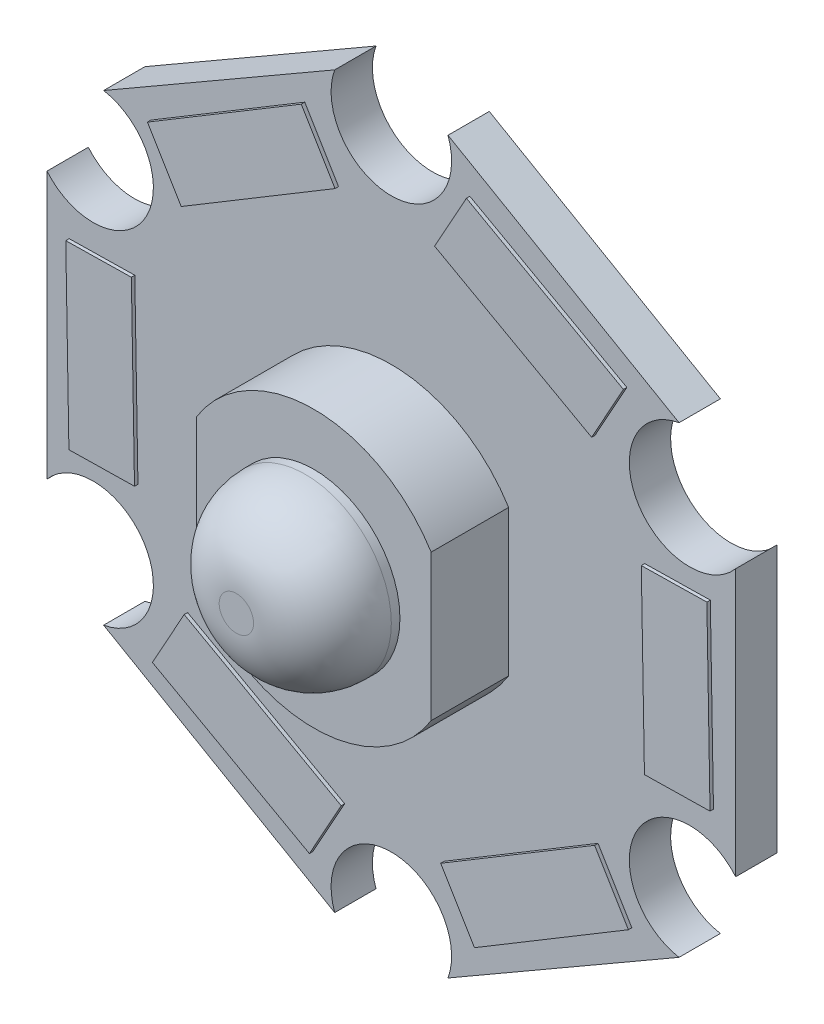
SolidWorks part; units mm, degrees
material "Aleación 1060"
ref_plane "Alzado" through (0, 0, 0) normal (0, 0, 1) x (1, 0, 0)
ref_plane "Planta" through (0, 0, 0) normal (0, 1, 0) x (1, 0, 0)
ref_plane "Vista lateral" through (0, 0, 0) normal (1, 0, 0) x (0, 0, -1)
sketch "Croquis1" plane through (0, 0, 0) normal (0, 0, 1) x (1, 0, 0)
  line L0 (8.6603, 5) -> (-8.6603, -5) construction
  line L1 (-10, 3.8741) -> (-10, -3.8741)
  line L2 (-8.3551, -6.7232) -> (-1.6449, -10.5973)
  line L3 (1.6449, -10.5973) -> (8.3551, -6.7232)
  line L4 (10, -3.8741) -> (10, 3.8741)
  line L5 (8.3551, 6.7232) -> (1.6449, 10.5973)
  line L6 (-1.6449, 10.5973) -> (-8.3551, 6.7232)
  line L7 (0, -9.75) -> (0, 0) construction
  line L8 (0, 0) -> (15.2259, 0) construction
  line L9 (0, 0) -> (0, 9.75) construction
  line L10 (-10, -5.7735) -> (-9.8984, -5.7891) construction
  circle A0 centre (0, 0) radius 10 construction
  arc A1 (8.3551, 6.7232) -> (10, 3.8741) centre (8.6603, 5) ccw
  arc A2 (10, -3.8741) -> (8.3551, -6.7232) centre (8.6603, -5) ccw
  arc A3 (1.6449, -10.5973) -> (-1.6449, -10.5973) centre (0, -10) ccw
  arc A4 (-8.3551, -6.7232) -> (-10, -3.8741) centre (-8.6603, -5) ccw
  arc A5 (-10, 3.8741) -> (-8.3551, 6.7232) centre (-8.6603, 5) ccw
  arc A6 (-1.6449, 10.5973) -> (1.6449, 10.5973) centre (0, 10) ccw
  point P28 (0, 0)
  dimension "D2" = 3.5
  dimension "D1" = 20
  dimension "D3" = 19.5
  dimension "D4" = 6
extrude "Saliente-Extruir1" add sketch "Croquis1" along normal blind 1.2
sketch "Croquis2" plane through (0, 0, 1.2) normal (0, 0, 1) x (1, 0, 0)
  line L0 (2.2798, 9.3802) -> (6.8394, 6.8532)
  line L1 (6.8394, 6.8532) -> (5.916, 5.1871)
  line L2 (5.916, 5.1871) -> (1.3564, 7.7141)
  line L3 (1.3564, 7.7141) -> (2.2798, 9.3802)
  line L4 (9.2634, 2.7157) -> (9.3547, -2.4965)
  line L5 (9.3547, -2.4965) -> (7.4501, -2.5299)
  line L6 (7.4501, -2.5299) -> (7.3588, 2.6823)
  line L7 (7.3588, 2.6823) -> (9.2634, 2.7157)
  line L8 (6.9836, -6.6645) -> (2.5153, -9.3497)
  line L9 (2.5153, -9.3497) -> (1.5341, -7.717)
  line L10 (1.5341, -7.717) -> (6.0024, -5.0317)
  line L11 (6.0024, -5.0317) -> (6.9836, -6.6645)
  line L12 (-2.2798, -9.3802) -> (-6.8394, -6.8532)
  line L13 (-6.8394, -6.8532) -> (-5.916, -5.1871)
  line L14 (-5.916, -5.1871) -> (-1.3564, -7.7141)
  line L15 (-1.3564, -7.7141) -> (-2.2798, -9.3802)
  line L16 (-9.2634, -2.7157) -> (-9.3547, 2.4965)
  line L17 (-9.3547, 2.4965) -> (-7.4501, 2.5299)
  line L18 (-7.4501, 2.5299) -> (-7.3588, -2.6823)
  line L19 (-7.3588, -2.6823) -> (-9.2634, -2.7157)
  line L20 (-6.9836, 6.6645) -> (-2.5153, 9.3497)
  line L21 (-2.5153, 9.3497) -> (-1.5341, 7.717)
  line L22 (-1.5341, 7.717) -> (-6.0024, 5.0317)
  line L23 (-6.0024, 5.0317) -> (-6.9836, 6.6645)
  point P26 (0, 0)
  dimension "D1" = 6
extrude "Saliente-Extruir2" add sketch "Croquis2" along normal blind 0.1 separate body
sketch "Croquis3" plane through (0, 0, 1.2) normal (0, 0, 1) x (1, 0, 0)
  line L0 (-3.4066, 2.1187) -> (-3.4066, -2.1187)
  line L1 (3.4066, 2.1187) -> (3.4066, -2.1187)
  arc A0 (-3.4066, -2.1187) -> (3.4066, -2.1187) centre (0, 0) ccw
  arc A1 (3.4066, 2.1187) -> (-3.4066, 2.1187) centre (0, 0) ccw
extrude "Saliente-Extruir3" add sketch "Croquis3" along normal blind 2.25 separate body
sketch "Croquis4" plane through (0, 0, 3.45) normal (0, 0, 1) x (1, 0, 0)
  circle A0 centre (0, 0) radius 2.5
extrude "Saliente-Extruir4" add sketch "Croquis4" along normal blind 2.25
fillet "Redondeo4" radius 2 1 edges at (2.5, 0, 5.7)
